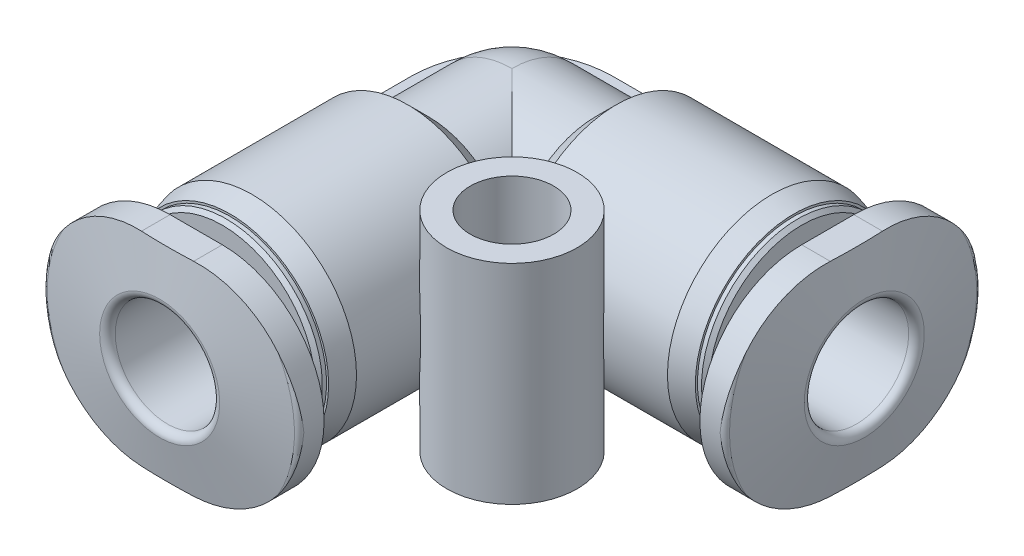
SolidWorks part; units mm, degrees
ref_plane "Ebene vorne" through (0, 0, 0) normal (0, 0, 1) x (1, 0, 0)
ref_plane "Ebene oben" through (0, 0, 0) normal (0, 1, 0) x (1, 0, 0)
ref_plane "Ebene rechts" through (0, 0, 0) normal (1, 0, 0) x (0, 0, -1)
sketch "Skizze1" plane through (0, 0, 0) normal (0, 0, 1) x (1, 0, 0)
  line L0 (0, 3.2) -> (3.2, 3.2)
  line L1 (3.2, 3.2) -> (4, 4)
  line L2 (4, 4) -> (9.9571, 4)
  line L3 (9.9571, 4) -> (10.8, 3.7742)
  line L4 (10.8, 3.7742) -> (10.8, 3.6938)
  line L5 (10.8, 3.6938) -> (10.9586, 3.6938)
  line L6 (10.9586, 3.6938) -> (11.1, 3.5524)
  line L7 (11.1, 3.5524) -> (11.1, 2.7)
  line L8 (11.1, 2.7) -> (11.73, 2.7)
  line L9 (12.1, 3.07) -> (12.1, 4.9)
  line L10 (12.1, 4.9) -> (12.8737, 4.9)
  line L11 (13.0707, 4.7347) -> (13.5, 2.3)
  line L12 (13.5, 2.3) -> (13.5, 0)
  line L13 (13.5, 0) -> (-3.2, 0)
  line L14 (13.5, 0) -> (-3.2, 0) construction
  arc A0 (-3.2, 0) -> (0, 3.2) centre (0, 0) cw
  arc A1 (11.73, 2.7) -> (12.1, 3.07) centre (11.73, 3.07) ccw
  arc A2 (12.8737, 4.9) -> (13.0707, 4.7347) centre (12.8737, 4.7) cw
revolve "Rotation1" add sketch "Skizze1" angle 360 about L14
ref_plane "Ebene1" through (13.5, 0, 0) normal (1, 0, 0) x (0, 0, -1)
sketch "Skizze2" plane through (13.5, 0, 0) normal (1, 0, 0) x (0, 0, -1)
  line L0 (-5.88, -3.3948) -> (0, -6.7896)
  line L1 (0, -6.7896) -> (5.88, -3.3948)
  line L2 (5.88, -3.3948) -> (5.88, 3.3948)
  line L3 (5.88, 3.3948) -> (0, 6.7896)
  line L4 (0, 6.7896) -> (-5.88, 3.3948)
  line L5 (-5.88, 3.3948) -> (-5.88, -3.3948)
  line L6 (-1, -3.9) -> (1, -3.9)
  line L7 (1, 3.9) -> (-1, 3.9)
  arc A0 (-4.9, 0) -> (-1, -3.9) centre (-1, 0) ccw
  arc A1 (1, -3.9) -> (4.9, 0) centre (1, 0) ccw
  arc A2 (4.9, 0) -> (1, 3.9) centre (1, 0) ccw
  arc A3 (-1, 3.9) -> (-4.9, 0) centre (-1, 0) ccw
extrude "Schnitt-Linear austragen1" cut sketch "Skizze2" against normal blind 1.4
sketch "Skizze3" plane through (0, 0, 0) normal (1, 0, 0) x (0, 0, -1)
  line L0 (-3.873, -1) -> (3.873, -1)
  line L1 (3.873, 1) -> (-3.873, 1)
  arc A0 (-3.873, 1) -> (-3.873, -1) centre (0, 0) ccw
  arc A1 (3.873, -1) -> (3.873, 1) centre (0, 0) ccw
extrude "Aufsatz-Linear austragen1" add sketch "Skizze3" along normal blind 4
sketch "Skizze4" plane through (0, 0, 0) normal (0, 1, 0) x (1, 0, 0)
  line L0 (0, 1.5) -> (2, 1.5)
  line L1 (2, 1.5) -> (2, 1.8)
  line L2 (2.2, 2) -> (13.2, 2)
  line L3 (13.5, 2.3) -> (13.5, 0)
  line L4 (13.5, 0) -> (-1.5, 0)
  line L5 (13.5, 0) -> (-1.5, 0) construction
  arc A0 (-1.5, 0) -> (0, 1.5) centre (0, 0) cw
  arc A1 (2, 1.8) -> (2.2, 2) centre (2.2, 1.8) cw
  arc A2 (13.2, 2) -> (13.5, 2.3) centre (13.2, 2.3) ccw
sketch "Skizze5" plane through (0, 0, 0) normal (0, 0, 1) x (1, 0, 0)
  line L0 (-3.873, -1) -> (0, -1)
  line L1 (0, -1) -> (0, 1)
  line L2 (0, 1) -> (-3.873, 1)
  arc A0 (-3.873, 1) -> (-3.873, -1) centre (0, 0) ccw
extrude "Aufsatz-Linear austragen2" add sketch "Skizze5" along normal blind 4
sketch "Skizze6" plane through (0, 0, 0) normal (1, 0, 0) x (0, 0, -1)
  line L0 (0, 0) -> (0, -3.2)
  line L1 (0, -3.2) -> (-3.2, -3.2)
  line L2 (-3.2, -3.2) -> (-4, -4)
  line L3 (-4, -4) -> (-9.9571, -4)
  line L4 (-9.9571, -4) -> (-10.8, -3.7742)
  line L5 (-10.8, -3.7742) -> (-10.8, -3.6938)
  line L6 (-10.8, -3.6938) -> (-10.9586, -3.6938)
  line L7 (-10.9586, -3.6938) -> (-11.1, -3.5524)
  line L8 (-11.1, -3.5524) -> (-11.1, -2.7)
  line L9 (-11.1, -2.7) -> (-11.73, -2.7)
  line L10 (-12.1, -3.07) -> (-12.1, -4.9)
  line L11 (-12.1, -4.9) -> (-12.8737, -4.9)
  line L12 (-13.0707, -4.7347) -> (-13.5, -2.3)
  line L13 (-13.5, -2.3) -> (-13.5, 0)
  line L14 (-13.5, 0) -> (0, 0)
  line L15 (-13.5, 0) -> (0, 0) construction
  arc A0 (-11.73, -2.7) -> (-12.1, -3.07) centre (-11.73, -3.07) ccw
  arc A1 (-12.8737, -4.9) -> (-13.0707, -4.7347) centre (-12.8737, -4.7) cw
revolve "Rotation2" add sketch "Skizze6" angle 360 about L15
ref_plane "Ebene2" through (0, 0, 13.5) normal (0, 0, 1) x (1, 0, 0)
sketch "Skizze7" plane through (0, 0, 13.5) normal (0, 0, 1) x (1, 0, 0)
  line L0 (-5.88, -3.3948) -> (0, -6.7896)
  line L1 (0, -6.7896) -> (5.88, -3.3948)
  line L2 (5.88, -3.3948) -> (5.88, 3.3948)
  line L3 (5.88, 3.3948) -> (0, 6.7896)
  line L4 (0, 6.7896) -> (-5.88, 3.3948)
  line L5 (-5.88, 3.3948) -> (-5.88, -3.3948)
  line L6 (-1, -3.9) -> (1, -3.9)
  line L7 (1, 3.9) -> (-1, 3.9)
  arc A0 (-4.9, 0) -> (-1, -3.9) centre (-1, 0) ccw
  arc A1 (1, -3.9) -> (4.9, 0) centre (1, 0) ccw
  arc A2 (4.9, 0) -> (1, 3.9) centre (1, 0) ccw
  arc A3 (-1, 3.9) -> (-4.9, 0) centre (-1, 0) ccw
extrude "Schnitt-Linear austragen2" cut sketch "Skizze7" against normal blind 1.4
sketch "Skizze8" plane through (0, 0, 0) normal (1, 0, 0) x (0, 0, -1)
  line L0 (0, 0) -> (0, -1.5)
  line L1 (0, -1.5) -> (-2, -1.5)
  line L2 (-2, -1.5) -> (-2, -1.8)
  line L3 (-2.2, -2) -> (-13.2, -2)
  line L4 (-13.5, -2.3) -> (-13.5, 0)
  line L5 (-13.5, 0) -> (0, 0)
  line L6 (-13.5, 0) -> (0, 0) construction
  arc A0 (-2, -1.8) -> (-2.2, -2) centre (-2.2, -1.8) cw
  arc A1 (-13.2, -2) -> (-13.5, -2.3) centre (-13.2, -2.3) ccw
sketch "Skizze9" plane through (0, 0, 0) normal (0, 1, 0) x (1, 0, 0)
  circle A0 centre (5.5, -5.5) radius 2.5
extrude "Aufsatz-Linear austragen3" add sketch "Skizze9" against normal blind 4 and the other way blind 4
hole_wizard "Bohrung1" positions "Skizze11" profile "Skizze10" legacy
sketch "Skizze11" plane through (0, 4, 0) normal (0, 1, 0) x (1, 0, 0)
  point P0 (5.5, -5.5)
sketch "Skizze10" plane through (5.5, 4, 5.5) normal (1, 0, 0) x (0, 0, 1)
  line L0 (0, 0) -> (0, 9)
  line L1 (0, 9) -> (1.6, 9)
  line L2 (1.6, 9) -> (1.6, 0)
  line L3 (1.6, 0) -> (0, 0)
  line L4 (0, 110) -> (0, -10) construction
  dimension "Durchmesser" = 3.2
  dimension "Tiefe" = 9
sketch "Skizze12" plane through (0, 0, 0) normal (1, 0, 0) x (0, 0, -1)
  line L0 (0, 1) -> (3.873, 1)
  line L1 (3.873, -1) -> (0, -1)
  line L2 (0, -1) -> (0, 1)
  line L3 (0, -1) -> (0, 1) construction
  arc A0 (3.873, 1) -> (3.873, -1) centre (0, 0) cw
revolve "Rotation3" add sketch "Skizze12" angle 90 about L3
revolve "Schnitt-Rotation1" cut sketch "Skizze8" angle 360 about L6
revolve "Schnitt-Rotation2" cut sketch "Skizze4" angle 360 about L5
